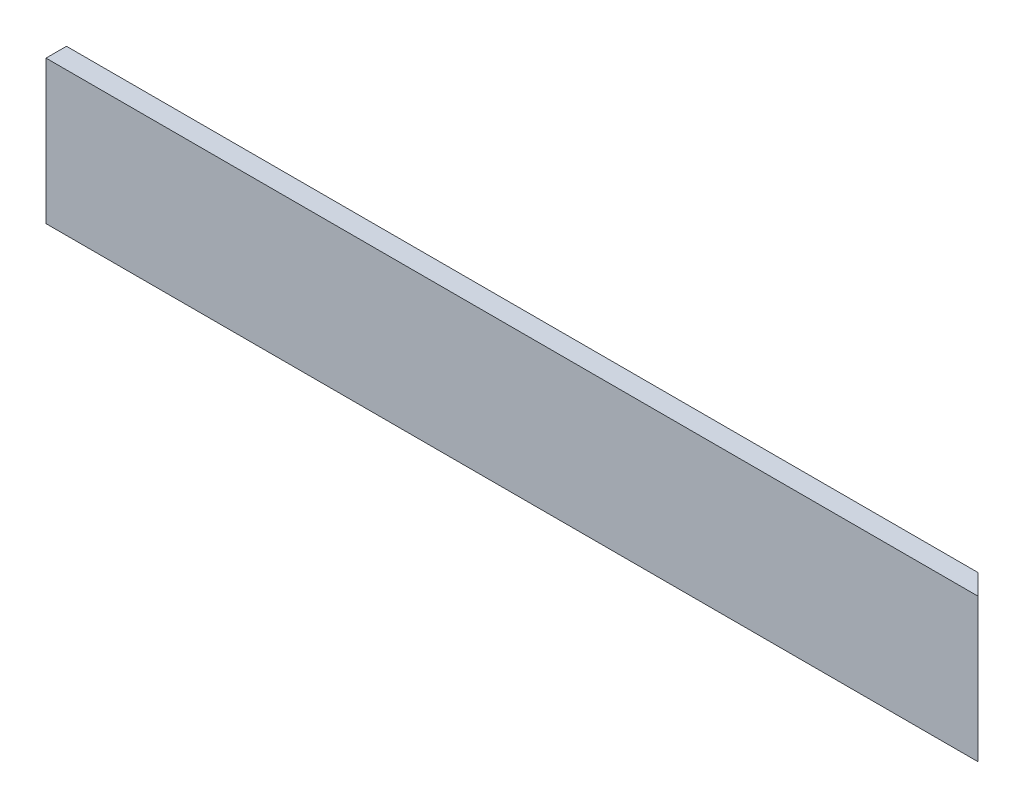
SolidWorks part; units mm, degrees
material "Cedar"
ref_plane "Front Plane" through (0, 0, 0) normal (0, 0, 1) x (1, 0, 0)
ref_plane "Top Plane" through (0, 0, 0) normal (0, 1, 0) x (1, 0, 0)
ref_plane "Right Plane" through (0, 0, 0) normal (1, 0, 0) x (0, 0, -1)
sketch "Sketch1" plane through (0, 0, 0) normal (0, 0, 1) x (1, 0, 0)
  line L1 (-180.9651, 22.1362) -> (396.8849, 22.1362)
  line L2 (-180.9651, 22.1362) -> (-180.9651, -66.7638)
  line L3 (-180.9651, -66.7638) -> (396.8849, -66.7638)
  line L4 (396.8849, 22.1362) -> (396.8849, -66.7638)
  dimension "D1" = 577.85
  dimension "D2" = 88.9
extrude "Boss-Extrude1" add sketch "Sketch1" along normal blind 12.7
sketch "Sketch2" plane through (0, 22.1362, 0) normal (0, 1, 0) x (1, 0, 0)
  line L0 (396.8849, -12.7) -> (384.1849, 0)
  line L1 (396.8849, 0) -> (-180.9651, 0) construction
  line L2 (384.1849, 0) -> (396.8849, 0)
  line L3 (396.8849, 0) -> (396.8849, -12.7)
  dimension "D1" = 45
extrude "Cut-Extrude1" cut sketch "Sketch2" against normal through all
